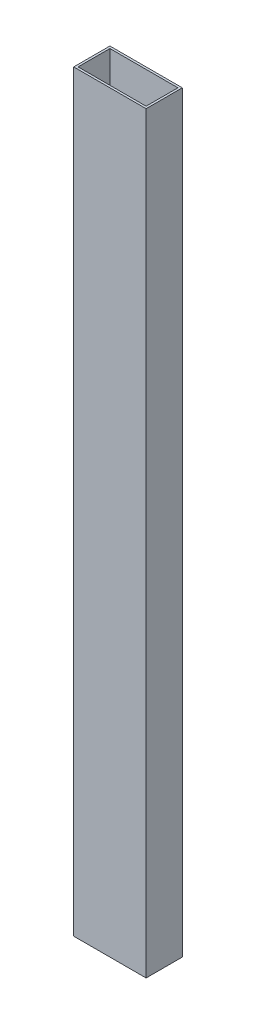
SolidWorks part; units mm, degrees
ref_plane "Front Plane" through (0, 0, 0) normal (0, 0, 1) x (1, 0, 0)
ref_plane "Top Plane" through (0, 0, 0) normal (0, 1, 0) x (1, 0, 0)
ref_plane "Right Plane" through (0, 0, 0) normal (1, 0, 0) x (0, 0, -1)
sketch "Sketch1" plane through (0, 0, 0) normal (0, 1, 0) x (1, 0, 0)
  line L1 (-9.0268, 20.7694) -> (41.7732, 20.7694)
  line L2 (-9.0268, 20.7694) -> (-9.0268, -4.6306)
  line L3 (-9.0268, -4.6306) -> (41.7732, -4.6306)
  line L4 (41.7732, 20.7694) -> (41.7732, -4.6306)
  line L5 (-7.5028, 19.2454) -> (40.2492, 19.2454)
  line L6 (-7.5028, 19.2454) -> (-7.5028, -3.1066)
  line L7 (-7.5028, -3.1066) -> (40.2492, -3.1066)
  line L8 (40.2492, 19.2454) -> (40.2492, -3.1066)
  dimension "D1" = 1.524
  dimension "D2" = 1.524
  dimension "D3" = 1.524
  dimension "D4" = 1.524
  dimension "D5" = 50.8
  dimension "D6" = 25.4
extrude "Boss-Extrude1" add sketch "Sketch1" along normal blind 528.32
